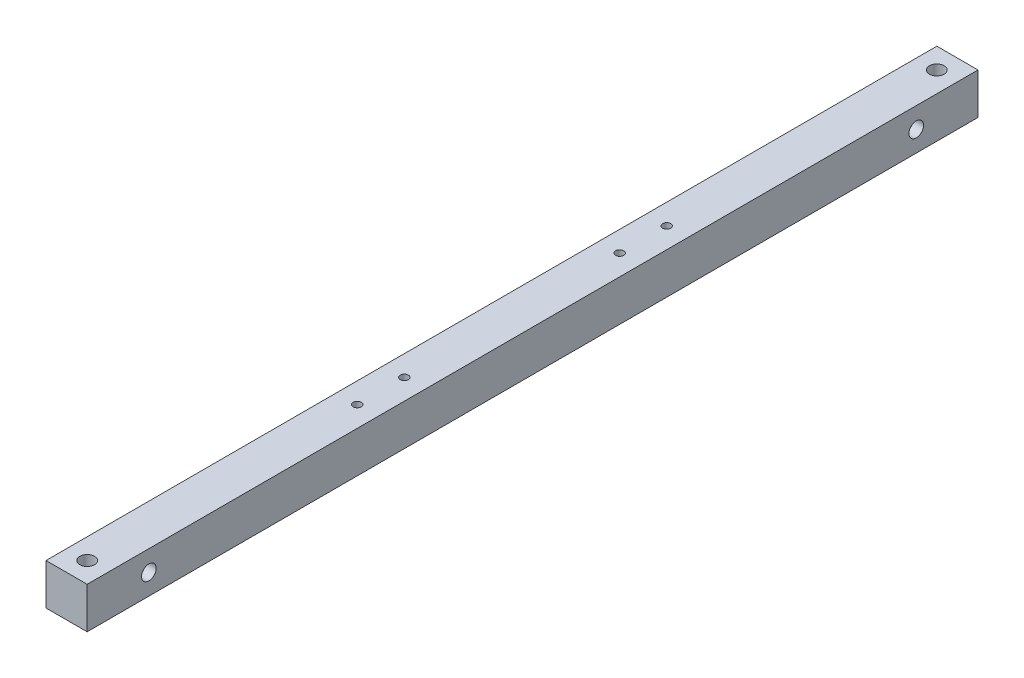
SolidWorks part; units mm, degrees
ref_plane "Ön Düzlem" through (0, 0, 0) normal (0, 0, 1) x (1, 0, 0)
ref_plane "Üst Düzlem" through (0, 0, 0) normal (0, 1, 0) x (1, 0, 0)
ref_plane "Sağ Düzlem" through (0, 0, 0) normal (1, 0, 0) x (0, 0, -1)
sketch "Çizim1" plane through (0, 0, 0) normal (0, 0, 1) x (1, 0, 0)
  line L1 (-14, -14) -> (14, -14)
  line L2 (-14, -14) -> (-14, 14)
  line L3 (-14, 14) -> (14, 14)
  line L4 (14, -14) -> (14, 14)
  line L5 (-14, -14) -> (14, 14) construction
  line L6 (-14, 14) -> (14, -14) construction
  point P0 (0, 0)
  dimension "D1" = 28
  dimension "D2" = 28
extrude "Yükseklik-Ekstrüzyon1" add sketch "Çizim1" along normal blind 606
sketch "Çizim2" plane through (14, 0, 0) normal (1, 0, 0) x (0, 0, -1)
  line L2 (0, -14) -> (0, 14) construction
  line L3 (-606, -14) -> (-606, 14) construction
  line L5 (-606, 14) -> (0, 14) construction
  circle A0 centre (-564, 0) radius 5
  circle A1 centre (-42, 0) radius 5
  dimension "D3" = 14
  dimension "D5" = 10
  dimension "D1" = 42
  dimension "D2" = 42
  dimension "D4" = 14
extrude "Kes-Ekstrüzyon1" cut sketch "Çizim2" against normal blind 7
sketch "Çizim3" plane through (14, 0, 0) normal (1, 0, 0) x (0, 0, -1)
  circle A0 centre (-564, 0) radius 3
  circle A1 centre (-42, 0) radius 3
  dimension "D1" = 6
extrude "Kes-Ekstrüzyon2" cut sketch "Çizim3" along direction (1, 0, 0) on the side against the normal through all and the other way through all
sketch "Çizim4" plane through (0, -14, 0) normal (0, -1, 0) x (1, 0, 0)
  line L0 (-14, 0) -> (14, 0) construction
  line L1 (-14, 606) -> (14, 606) construction
  circle A0 centre (0, 14) radius 3
  circle A1 centre (0, 592) radius 3
  dimension "D3" = 6
  dimension "D1" = 14
  dimension "D2" = 14
extrude "Kes-Ekstrüzyon3" cut sketch "Çizim4" against normal up to next
sketch "Çizim6" plane through (0, 14, 0) normal (0, 1, 0) x (1, 0, 0)
  circle A0 centre (0, -592) radius 5
  circle A1 centre (0, -14) radius 5
  dimension "D1" = 10
extrude "Kes-Ekstrüzyon5" cut sketch "Çizim6" against normal blind 7
sketch "Çizim7" plane through (0, 14, 0) normal (0, 1, 0) x (1, 0, 0)
  line L0 (-14, -606) -> (-14, 0) construction
  line L1 (-14, -606) -> (-14, 0) construction
  line L2 (-14, -303) -> (14, -303) construction
  line L3 (14, -606) -> (14, 0) construction
  line L4 (0, -408.25) -> (0, -376.25) construction
  circle A0 centre (0, -408.25) radius 2.75
  circle A1 centre (0, -376.25) radius 2.75
  circle A2 centre (0, -229.75) radius 2.75
  circle A3 centre (0, -197.75) radius 2.75
  point P10 (0, -392.25)
  point P11 (0, -303)
  dimension "D1" = 32
  dimension "D2" = 5.5
  dimension "D3" = 89.25
extrude "Kes-Ekstrüzyon6" cut sketch "Çizim7" against normal through all
